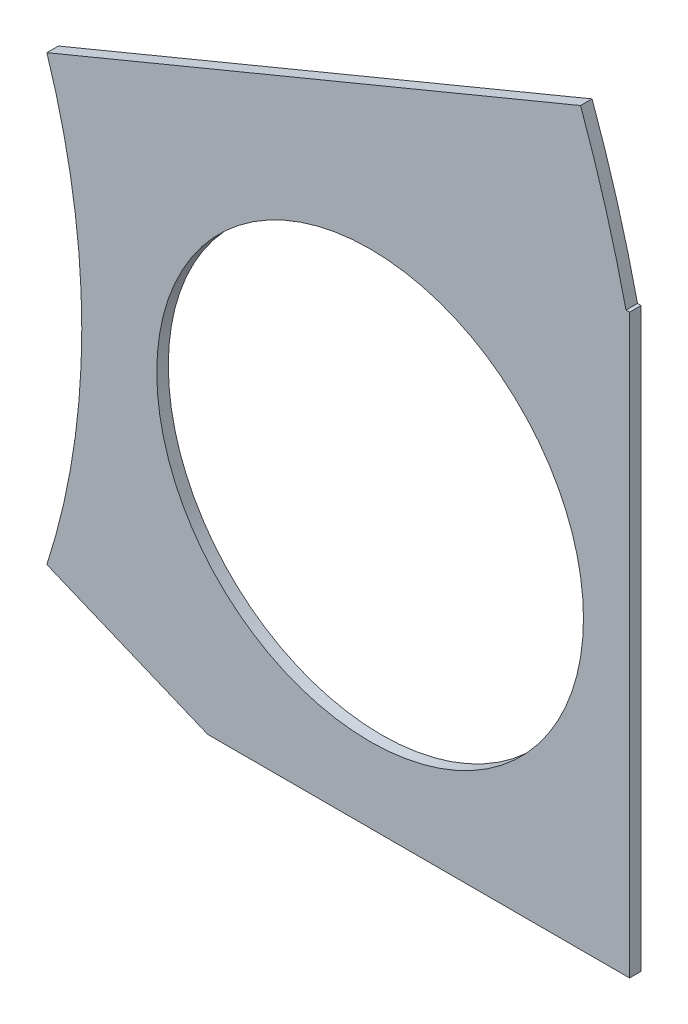
SolidWorks part; units mm, degrees
material "Copper"
ref_plane "Front Plane" through (0, 0, 0) normal (0, 0, 1) x (1, 0, 0)
ref_plane "Top Plane" through (0, 0, 0) normal (0, 1, 0) x (1, 0, 0)
ref_plane "Right Plane" through (0, 0, 0) normal (1, 0, 0) x (0, 0, -1)
sketch "Sketch1" plane through (0, 0, 0) normal (0, 0, 1) x (1, 0, 0)
  line L0 (0, 0) -> (320.3893, 0) construction
  line L1 (0, 0) -> (155.5285, 155.5285) construction
  line L2 (67.2115, 76.1917) -> (8.6967, 17.6769)
  line L3 (8.6967, 17.6769) -> (7.229, 14.1336)
  line L4 (101.4014, -6.35) -> (18.6489, -6.35)
  line L5 (15.1056, -4.8823) -> (18.6489, -6.35)
  line L6 (88.6729, 6.35) -> (27.8605, 6.35)
  line L9 (67.1914, 58.2111) -> (24.1905, 15.2102)
  line L10 (0, 0) -> (40.4486, 97.6516) construction
  line L11 (0, 0) -> (123.4567, -51.1374) construction
  line L18 (8.6967, 17.6769) -> (13.294, 8.6183) construction
  line L19 (18.6489, -6.35) -> (15.4943, 3.3063) construction
  line L20 (27.8605, 6.35) -> (27.7442, 6.7059) construction
  line L21 (24.1905, 15.2102) -> (24.3599, 14.8764) construction
  arc A0 (7.229, 14.1336) -> (15.1056, -4.8823) centre (0, 0) cw
  arc A1 (67.2115, 76.1917) -> (101.4014, -6.35) centre (0, 0) cw
  arc A2 (24.1905, 15.2102) -> (27.8605, 6.35) centre (0, 0) cw
  arc A3 (67.1914, 58.2111) -> (88.6729, 6.35) centre (0, 0) cw
  arc A8 (13.294, 8.6183) -> (15.4943, 3.3063) centre (0, 0) cw construction
  arc A9 (24.3599, 14.8764) -> (27.7442, 6.7059) centre (0, 0) cw construction
  dimension "D1" = 45
  dimension "D3" = 6.35
  dimension "D4" = 15.875
  dimension "D7" = 22.5
  dimension "D8" = 101.6
  dimension "D11" = 12.7
  dimension "D12" = 12.7
  dimension "D2" = 6.35
  dimension "D5" = 67.5
  dimension "D9" = 1.27
  dimension "D10" = 1.27
  dimension "D6" = 12.7
extrude "Boss-Extrude1" add sketch "Sketch1" along normal blind 0.254
sketch "Sketch2" plane through (0, 0, 0.254) normal (0, 0, 1) x (1, 0, 0)
  line L0 (0, 0) -> (101.6, 0) construction
  line L1 (0, 0) -> (71.842, 71.842) construction
  line L3 (0, 0) -> (22.225, 0) construction
  line L4 (0, 0) -> (15.7154, 15.7154) construction
  line L5 (0, 0) -> (95.25, 0) construction
  line L6 (0, 0) -> (92.0044, 24.6525) construction
  arc A0 (101.4014, -6.35) -> (67.2115, 76.1917) centre (0, 0) ccw construction
  circle A1 centre (22.225, 0) radius 4.699
  arc A2 (15.1056, -4.8823) -> (7.229, 14.1336) centre (0, 0) ccw construction
  circle A3 centre (36.195, 0) radius 4.699
  circle A4 centre (61.722, 0) radius 4.699
  circle A5 centre (75.692, 0) radius 4.699
  circle A6 centre (95.25, 0) radius 4.699
  circle A7 centre (15.7154, 15.7154) radius 4.699
  circle A8 centre (25.5937, 25.5937) radius 4.699
  circle A9 centre (43.644, 43.644) radius 4.699
  circle A10 centre (53.5223, 53.5223) radius 4.699
  circle A11 centre (92.0044, 24.6525) radius 4.699
  circle A12 centre (82.4889, 47.625) radius 4.699
  circle A13 centre (67.3519, 67.3519) radius 4.699
  dimension "D3" = 9.398
  dimension "D1" = 45
  dimension "D2" = 6.35
  dimension "D4" = 6.35
  dimension "D5" = 13.97
  dimension "D7" = 13.97
  dimension "D8" = 19.558
  dimension "D9" = 45
  dimension "D10" = 15
  dimension "D11" = 25.527
  dimension "D6" = 2
extrude "Cut-Extrude1" cut sketch "Sketch2" against normal through all
sketch "Sketch3" plane through (0, 0, 0.254) normal (0, 0, 1) x (1, 0, 0)
  line L0 (15.2664, 24.2467) -> (17.0625, 26.0427)
  line L1 (15.2664, 24.2467) -> (15.7154, 23.7977)
  line L2 (17.0625, 26.0427) -> (17.5115, 25.5937)
  line L3 (15.7154, 23.7977) -> (17.5115, 25.5937)
  line L4 (67.2115, 76.1917) -> (8.6967, 17.6769) construction
  line L5 (44.9911, 53.9713) -> (43.195, 52.1753)
  line L6 (44.9911, 53.9713) -> (45.4401, 53.5223)
  line L7 (43.195, 52.1753) -> (43.644, 51.7263)
  line L8 (45.4401, 53.5223) -> (43.644, 51.7263)
  line L9 (27.94, -6.35) -> (30.48, -6.35)
  line L10 (27.94, -6.35) -> (27.94, -5.715)
  line L11 (30.48, -6.35) -> (30.48, -5.715)
  line L12 (27.94, -5.715) -> (30.48, -5.715)
  line L13 (18.6489, -6.35) -> (101.4014, -6.35) construction
  line L14 (67.437, -6.35) -> (69.977, -6.35)
  line L15 (67.437, -6.35) -> (67.437, -5.715)
  line L16 (69.977, -6.35) -> (69.977, -5.715)
  line L17 (67.437, -5.715) -> (69.977, -5.715)
  line L18 (29.2307, 38.211) -> (31.0268, 40.007)
  line L19 (29.2307, 38.211) -> (29.6797, 37.762)
  line L20 (31.0268, 40.007) -> (31.4758, 39.558)
  line L21 (29.6797, 37.762) -> (31.4758, 39.558)
  line L22 (56.845, 65.8253) -> (55.049, 64.0292)
  line L23 (56.845, 65.8253) -> (57.294, 65.3763)
  line L24 (55.049, 64.0292) -> (55.498, 63.5802)
  line L25 (57.294, 65.3763) -> (55.498, 63.5802)
  line L26 (47.6885, -6.35) -> (50.2285, -6.35)
  line L27 (47.6885, -6.35) -> (47.6885, -5.715)
  line L28 (50.2285, -6.35) -> (50.2285, -5.715)
  line L29 (47.6885, -5.715) -> (50.2285, -5.715)
  line L30 (84.201, -6.35) -> (86.741, -6.35)
  line L31 (84.201, -6.35) -> (84.201, -5.715)
  line L32 (86.741, -6.35) -> (86.741, -5.715)
  line L33 (84.201, -5.715) -> (86.741, -5.715)
  line L34 (0, 0) -> (100.7308, 13.2615) construction
  line L35 (0, 0) -> (93.8662, 38.8806) construction
  line L36 (0, 0) -> (80.6047, 61.8502) construction
  line L37 (0, 0) -> (101.6, 0) construction
  line L38 (99.9355, 14.4377) -> (100.267, 11.9194)
  line L39 (99.9355, 14.4377) -> (101.1946, 14.6035)
  line L40 (100.267, 11.9194) -> (101.5261, 12.0852)
  line L41 (101.1946, 14.6035) -> (101.5261, 12.0852)
  line L42 (99.9355, 14.4377) -> (101.5261, 12.0852) construction
  line L43 (100.267, 11.9194) -> (101.1946, 14.6035) construction
  line L44 (93.7655, 37.4643) -> (94.9388, 37.9503)
  line L45 (93.7655, 37.4643) -> (92.7935, 39.811)
  line L46 (94.9388, 37.9503) -> (93.9668, 40.297)
  line L47 (92.7935, 39.811) -> (93.9668, 40.297)
  line L48 (93.7655, 37.4643) -> (93.9668, 40.297) construction
  line L49 (94.9388, 37.9503) -> (92.7935, 39.811) construction
  line L50 (79.3278, 62.4712) -> (80.874, 60.456)
  line L51 (79.3278, 62.4712) -> (80.3354, 63.2443)
  line L52 (80.874, 60.456) -> (81.8816, 61.2292)
  line L53 (80.3354, 63.2443) -> (81.8816, 61.2292)
  line L54 (79.3278, 62.4712) -> (81.8816, 61.2292) construction
  line L55 (80.874, 60.456) -> (80.3354, 63.2443) construction
  line L56 (13.5939, 7.0054) -> (14.5659, 4.6588)
  line L57 (13.5939, 7.0054) -> (14.7672, 7.4914)
  line L58 (14.5659, 4.6588) -> (15.7393, 5.1448)
  line L59 (14.7672, 7.4914) -> (15.7393, 5.1448)
  line L60 (13.5939, 7.0054) -> (15.7393, 5.1448) construction
  line L61 (14.5659, 4.6588) -> (14.7672, 7.4914) construction
  circle A0 centre (15.7154, 15.7154) radius 4.699 construction
  circle A1 centre (43.644, 43.644) radius 4.699 construction
  circle A2 centre (22.225, 0) radius 4.699 construction
  circle A3 centre (61.722, 0) radius 4.699 construction
  arc A4 (101.4014, -6.35) -> (67.2115, 76.1917) centre (0, 0) ccw construction
  arc A9 (15.1056, -4.8823) -> (7.229, 14.1336) centre (0, 0) ccw construction
  circle A10 centre (36.195, 0) radius 4.699 construction
  circle A11 centre (75.692, 0) radius 4.699 construction
  circle A12 centre (25.5937, 25.5937) radius 4.699 construction
  circle A13 centre (53.5223, 53.5223) radius 4.699 construction
  point P75 (14.6666, 6.0751)
  dimension "D2" = 5.715
  dimension "D3" = 2.54
  dimension "D6" = 5.715
  dimension "D8" = 0.635
  dimension "D9" = 5.715
  dimension "D12" = 5.715
  dimension "D4" = 7.5
  dimension "D5" = 22.5
  dimension "D7" = 37.5
  dimension "D10" = 90
  dimension "D11" = 1.27
  dimension "D14" = 0.635
  dimension "D15" = 90
  dimension "D18" = 0.635
  dimension "D19" = 90
  dimension "D22" = 0.635
  dimension "D20" = 1.27
  dimension "D17" = 0.635
  dimension "D13" = 11.4935
  dimension "D16" = 8.509
  dimension "D21" = 11.4935
  dimension "D23" = 8.509
extrude "Cut-Extrude2" cut sketch "Sketch3" against normal through all
sketch "Sketch5" plane through (0, 0, 0.254) normal (0, 0, 1) x (1, 0, 0)
  line L0 (11.5134, 3.3944) -> (27.94, 10.1985)
  line L1 (27.94, 10.1985) -> (27.94, -7.62)
  line L2 (27.94, -7.62) -> (11.5134, -7.62)
  line L3 (14.7672, 7.4914) -> (14.1336, 7.229) construction
  line L4 (11.5134, -7.62) -> (11.5134, 3.3944)
  line L5 (18.6489, -6.35) -> (27.94, -6.35) construction
  line L8 (30.48, -6.35) -> (30.48, -5.715) construction
  dimension "D1" = 2.54
  dimension "D2" = 1.27
  dimension "D3" = 2.54
  dimension "D4" = 17.78
extrude "Cut-Extrude5" cut sketch "Sketch5" against normal through all flip side to cut
equation "\"cSep\"= 1.005"
equation "\"D11@Sketch2\"=\"cSep\""
equation "\"cSep2\"= \"D8@Sketch2\""
equation "\"D13@Sketch3\"=\"cSep\"/2-.05"
equation "\"D16@Sketch3\"=\"cSep2\"/2-.05"
equation "\"D21@Sketch3\"=\"cSep\"/2-.05"
equation "\"D23@Sketch3\"=\"cSep2\"/2-.05"
